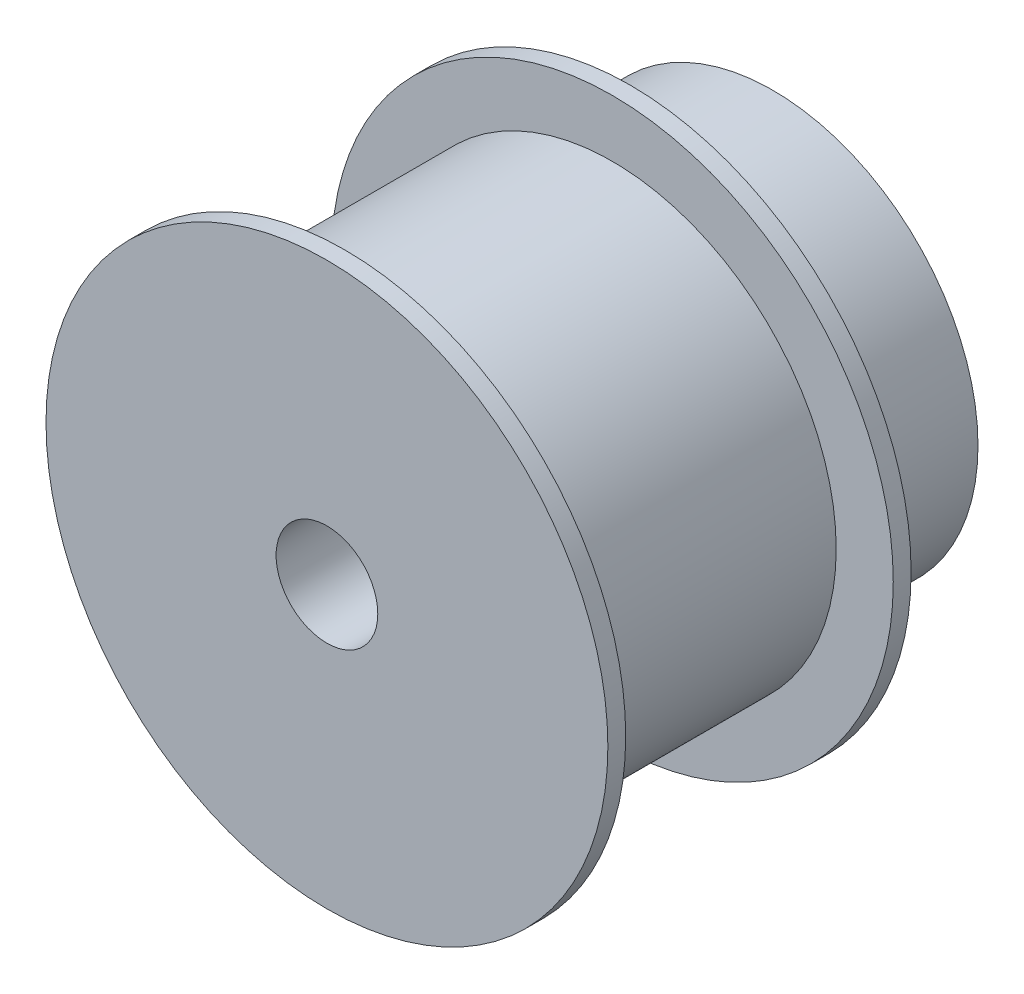
SolidWorks part; units mm, degrees
ref_plane "Plan de face" through (0, 0, 0) normal (0, 0, 1) x (1, 0, 0)
ref_plane "Plan de dessus" through (0, 0, 0) normal (0, 1, 0) x (1, 0, 0)
ref_plane "Plan de droite" through (0, 0, 0) normal (1, 0, 0) x (0, 0, -1)
sketch "Esquisse1" plane through (0, 0, 0) normal (0, 1, 0) x (1, 0, 0)
  line L0 (15.75, -9) -> (15.75, -8)
  line L1 (15.75, -8) -> (11.5, -8)
  line L2 (11.5, -8) -> (11.5, 0)
  line L3 (11.5, 0) -> (2.85, 0)
  line L4 (2.85, 0) -> (2.85, -25)
  line L5 (2.85, -25) -> (15.75, -25)
  line L6 (15.75, -25) -> (15.75, -24)
  line L7 (15.75, -24) -> (12.55, -24)
  line L8 (12.55, -24) -> (12.55, -9)
  line L9 (12.55, -9) -> (15.75, -9)
  line L10 (0, 0) -> (0, -25) construction
revolve "Révolution1" add sketch "Esquisse1" angle 360 about L10
